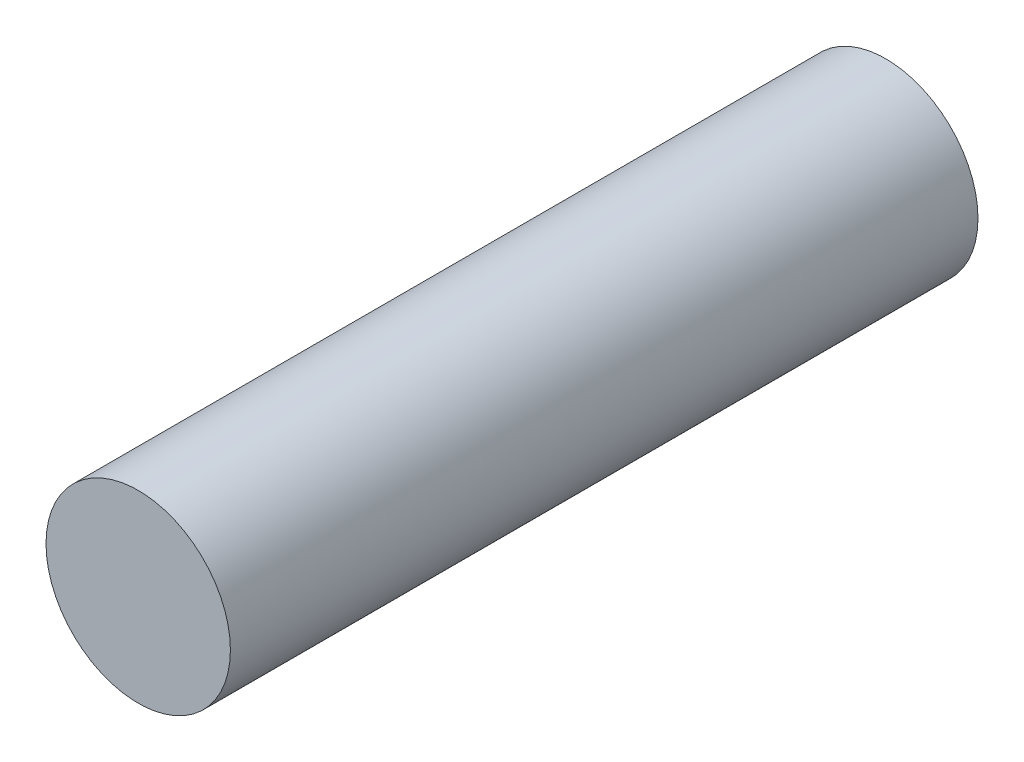
SolidWorks part; units mm, degrees
ref_plane "Front" through (0, 0, 0) normal (0, 0, 1) x (1, 0, 0)
ref_plane "Top" through (0, 0, 0) normal (0, 1, 0) x (1, 0, 0)
ref_plane "Right" through (0, 0, 0) normal (1, 0, 0) x (0, 0, -1)
other "Configuration Table"
sketch "Sketch1" plane through (0, 0, 0) normal (0, 0, 1) x (1, 0, 0)
  circle A0 centre (0, 0) radius 4.699
  dimension "D1" = 9.398
extrude "Base-Extrude" add sketch "Sketch1" along normal blind 38.1
